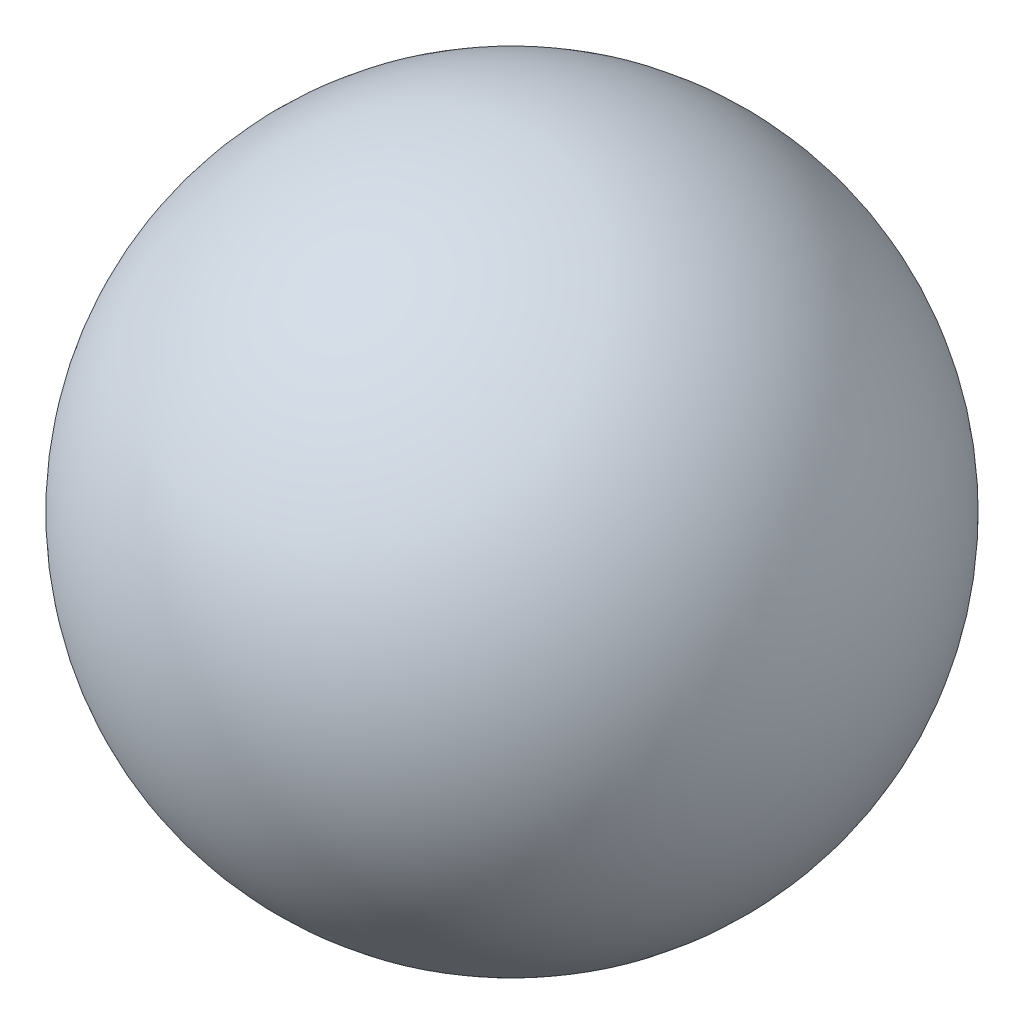
SolidWorks part; units mm, degrees
material "Rubber"
ref_plane "Front Plane" through (0, 0, 0) normal (0, 0, 1) x (1, 0, 0)
ref_plane "Top Plane" through (0, 0, 0) normal (0, 1, 0) x (1, 0, 0)
ref_plane "Right Plane" through (0, 0, 0) normal (1, 0, 0) x (0, 0, -1)
sketch "Sketch1" plane through (0, 0, 0) normal (0, 0, 1) x (1, 0, 0)
  line L0 (0, -3.25) -> (0, 3.25)
  arc A0 (0, 3.25) -> (0, -3.25) centre (0, 0) cw
  point P6 (0, 0)
  dimension "D1" = 6.5
revolve "Revolve1" add sketch "Sketch1" angle 360 about L0
